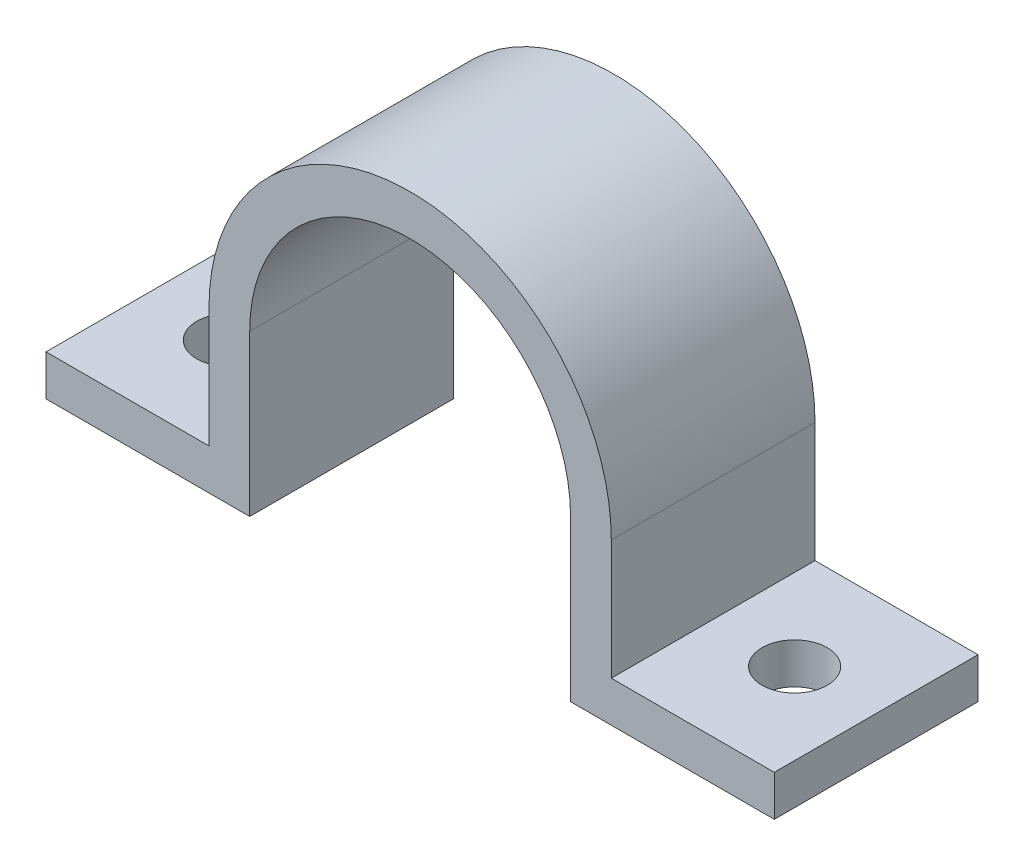
SolidWorks part; units mm, degrees
material "AISI 1020"
ref_plane "Front Plane" through (0, 0, 0) normal (0, 0, 1) x (1, 0, 0)
ref_plane "Top Plane" through (0, 0, 0) normal (0, 1, 0) x (1, 0, 0)
ref_plane "Right Plane" through (0, 0, 0) normal (1, 0, 0) x (0, 0, -1)
sketch "Sketch1" plane through (0, 0, 0) normal (0, 0, 1) x (1, 0, 0)
  line L0 (-9.1635, -0.0026) -> (-9.1635, -10.0026)
  line L1 (10.8365, -0.0026) -> (10.8365, -10.0026)
  line L2 (-9.1635, -10.0026) -> (-21.8635, -10.0026)
  line L3 (10.8365, -10.0026) -> (23.5365, -10.0026)
  line L4 (-21.8635, -7.4626) -> (-11.7035, -7.4626)
  line L5 (23.5365, -10.0026) -> (23.5365, -7.4626)
  line L6 (13.3765, -7.4626) -> (23.5365, -7.4626)
  line L7 (-21.8635, -10.0026) -> (-21.8635, -7.4626)
  line L10 (-11.7035, -0.0026) -> (-11.7035, -7.4626)
  line L12 (13.3765, -0.0026) -> (13.3765, -7.4626)
  arc A0 (-9.1635, -0.0026) -> (10.8365, -0.0026) centre (0.8365, -0.0026) cw
  arc A1 (-11.7035, -0.0026) -> (13.3765, -0.0026) centre (0.8365, -0.0026) cw
  dimension "D1" = 20
  dimension "D2" = 10
  dimension "D3" = 12.7
  dimension "D4" = 12.7
  dimension "D5" = 2.54
  dimension "D7" = 2.54
  dimension "D8" = 2.54
  dimension "D9" = 2.54
extrude "Boss-Extrude1" add sketch "Sketch1" along normal blind 12.7
sketch "Sketch3" plane through (0, -7.4626, 0) normal (0, 1, 0) x (1, 0, 0)
  line L1 (23.5365, -12.7) -> (23.5365, 0) construction
  line L2 (-21.8635, -12.7) -> (-21.8635, 0) construction
  line L3 (-11.7035, 0) -> (-21.8635, 0) construction
  line L4 (23.5365, 0) -> (13.3765, 0) construction
  circle A0 centre (-16.7835, -6.35) radius 2.032
  circle A1 centre (18.4565, -6.35) radius 2.032
  dimension "D1" = 4.064
  dimension "D2" = 4.064
  dimension "D3" = 5.08
  dimension "D4" = 5.08
  dimension "D5" = 6.35
  dimension "D6" = 6.35
extrude "Cut-Extrude1" cut sketch "Sketch3" against normal blind 12.7
